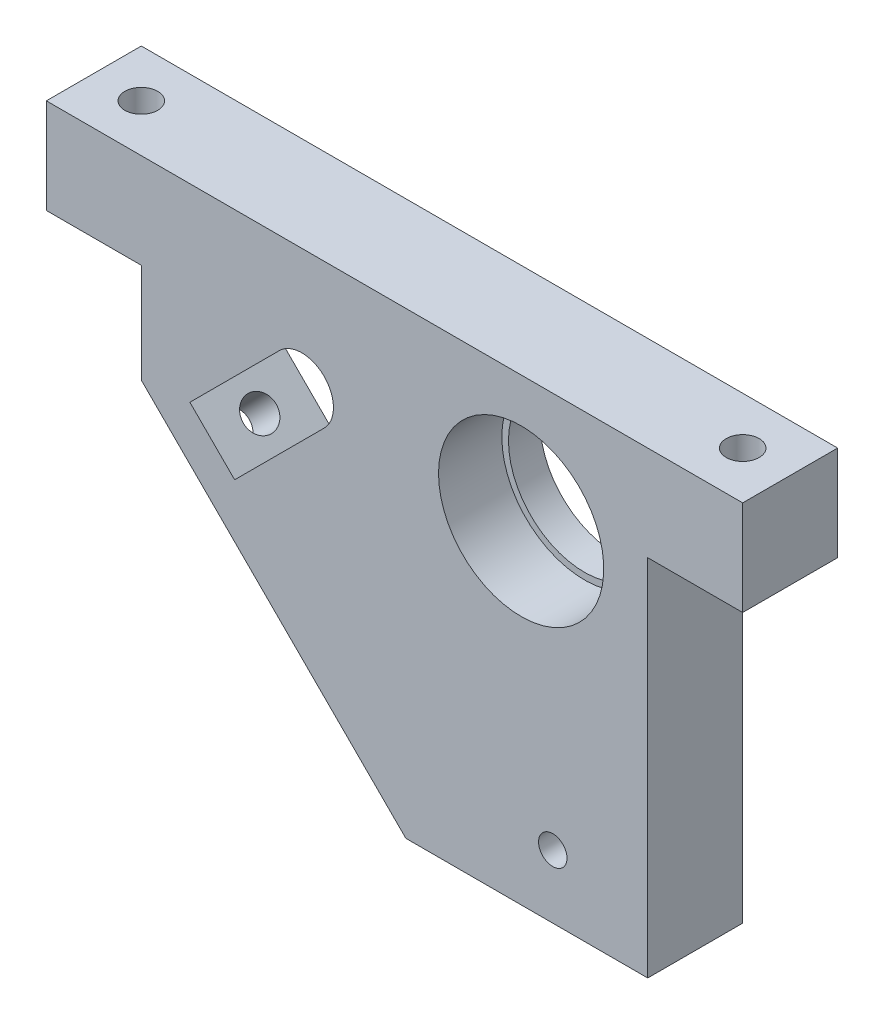
SolidWorks part; units mm, degrees
ref_plane "前视基准面" through (0, 0, 0) normal (0, 0, 1) x (1, 0, 0)
ref_plane "上视基准面" through (0, 0, 0) normal (0, 1, 0) x (1, 0, 0)
ref_plane "右视基准面" through (0, 0, 0) normal (1, 0, 0) x (0, 0, -1)
sketch "草图1" plane through (0, 0, 0) normal (0, 0, 1) x (1, 0, 0)
  line L0 (-33.801, 26.3835) -> (-27.4406, 26.3835)
  line L1 (-33.801, 41.3835) -> (56.199, 41.3835)
  line L2 (-33.801, 41.3835) -> (-33.801, 26.3835)
  line L3 (22.9883, -31.1165) -> (61.199, -31.1165)
  line L5 (-18.801, 10.6728) -> (22.9883, -31.1165)
  line L7 (-28.6333, -13.0935) -> (32.4873, 48.0271) construction
  line L8 (-11.1269, 11.484) -> (3.0152, 25.6261)
  line L9 (6.5876, -21.1165) -> (83.4627, -21.1165) construction
  line L10 (-4.0558, 4.4129) -> (10.0863, 18.5551)
  line L11 (46.199, -4.7233) -> (46.199, -58.0817) construction
  line L12 (-27.4406, 26.3835) -> (-18.801, 26.3835)
  line L13 (-18.801, 26.3835) -> (-18.801, 10.6728)
  line L14 (56.199, 41.3835) -> (76.199, 41.3835)
  line L15 (76.199, 41.3835) -> (76.199, 26.3835)
  line L16 (76.199, 26.3835) -> (61.199, 26.3835)
  line L17 (61.199, 26.3835) -> (61.199, -31.1165)
  line L19 (-11.1269, 11.484) -> (-4.0558, 4.4129)
  circle A0 centre (41.199, 21.3835) radius 12
  circle A1 centre (41.199, 21.3835) radius 25 construction
  arc A3 (10.0863, 18.5551) -> (3.0152, 25.6261) centre (6.5508, 22.0906) ccw
  circle A4 centre (46.199, -21.1165) radius 2.25
  dimension "D3" = 50
  dimension "D4" = 24
  dimension "D5" = 20
  dimension "D6" = 20
  dimension "D8" = 50
  dimension "D13" = 6
  dimension "D14" = 5
  dimension "D15" = 20
  dimension "D17" = 4.5
  dimension "D7" = 45
  dimension "D9" = 15
  dimension "D10" = 15
  dimension "D11" = 45
  dimension "D12" = 25
  dimension "D16" = 10
  dimension "D18" = 15
  dimension "D19" = 15
  dimension "D20" = 15
  dimension "D21" = 110
  dimension "D22" = 72.5
extrude "凸台-拉伸1" add sketch "草图1" along normal blind 15
sketch "草图2" plane through (0, 0, 15) normal (0, 0, -1) x (-1, 0, 0)
  circle A0 centre (-41.199, 21.3835) radius 13.05
  dimension "D1" = 26.1
extrude "切除-拉伸1" cut sketch "草图2" along normal blind 10
sketch "草图3" plane through (0, 41.3835, 0) normal (0, 1, 0) x (1, 0, 0)
  line L0 (-45.1664, -7.5) -> (87.6779, -7.5) construction
  line L1 (76.199, 0) -> (-33.801, 0) construction
  line L2 (76.199, -15) -> (-33.801, -15) construction
  line L3 (-33.801, -15) -> (-33.801, 0) construction
  line L4 (76.199, -15) -> (76.199, 0) construction
  circle A0 centre (-26.301, -7.5) radius 2.6
  circle A1 centre (68.699, -7.5) radius 2.6
  dimension "D1" = 5.2
  dimension "D2" = 7.5
  dimension "D3" = 7.5
extrude "切除-拉伸2" cut sketch "草图3" against normal through all
sketch "草图5" plane through (-4.0641, -4.0641, 0) normal (-0.7071, -0.7071, 0) x (0, 0, 1)
  line L0 (-9.1574, 10.9911) -> (29.9899, 10.9911) construction
  line L1 (7.5, 30.0407) -> (7.5, -16.3526) construction
  line L2 (0, 20.8411) -> (0, -38.2579) construction
  line L3 (15, 20.8411) -> (15, -38.2579) construction
  line L4 (15, 20.8411) -> (0, 20.8411) construction
  circle A0 centre (7.5, 10.9911) radius 2.6
  dimension "D2" = 5.2
  dimension "D1" = 9.85
extrude "切除-拉伸3" cut sketch "草图5" against normal blind 10
